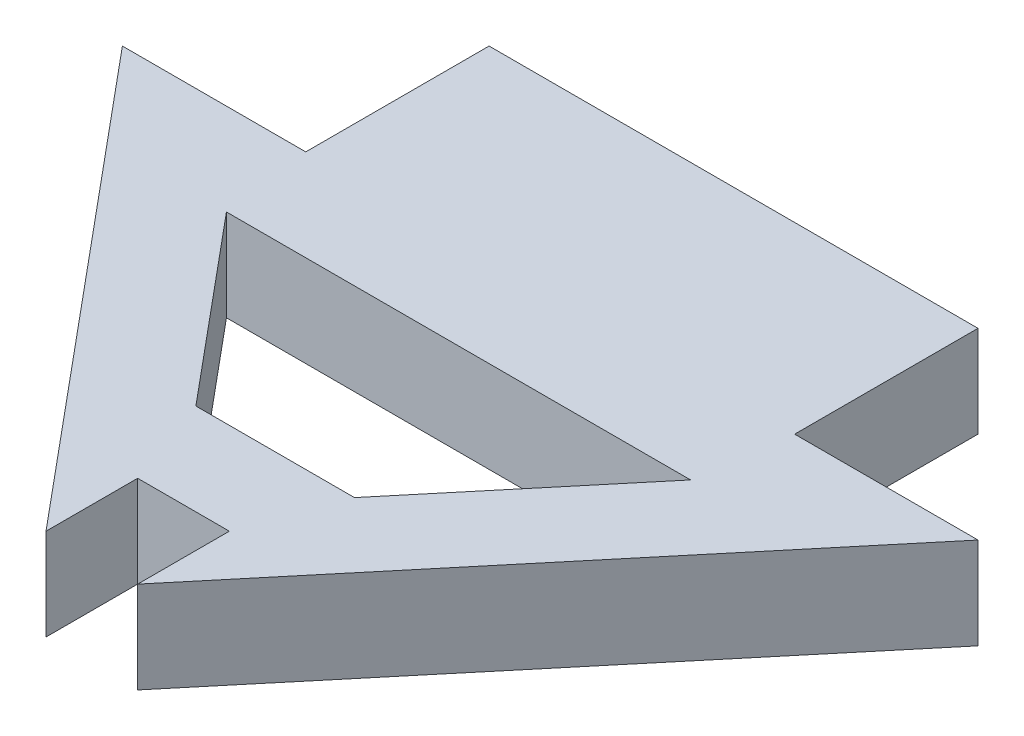
SolidWorks part; units mm, degrees
material "Custom Plastic"
ref_plane "Front Plane" through (0, 0, 0) normal (0, 0, 1) x (1, 0, 0)
ref_plane "Top Plane" through (0, 0, 0) normal (0, 1, 0) x (1, 0, 0)
ref_plane "Right Plane" through (0, 0, 0) normal (1, 0, 0) x (0, 0, -1)
sketch "Sketch1" plane through (0, 0, 0) normal (0, 1, 0) x (1, 0, 0)
  line L0 (22.0795, 3.0287) -> (16.0795, 3.0287)
  line L1 (16.0795, 3.0287) -> (16.0795, 9.0287)
  line L2 (16.0795, 9.0287) -> (0.0795, 9.0287)
  line L3 (0.0795, 9.0287) -> (0.0795, 3.0287)
  line L4 (0.0795, 3.0287) -> (-5.9205, 3.0287)
  line L5 (-5.9205, 3.0287) -> (6.5795, -11.9713)
  line L6 (6.5795, -11.9713) -> (6.5795, -8.9713)
  line L7 (6.5795, -8.9713) -> (9.5795, -8.9713)
  line L8 (9.5795, -8.9713) -> (9.5795, -11.9713)
  line L9 (9.5795, -11.9713) -> (22.0795, 3.0287)
  line L10 (8.0795, 9.0287) -> (8.0795, -8.9713) construction
  line L11 (9.5795, -11.9713) -> (6.5795, -11.9713) construction
  line L12 (15.6744, 0.0287) -> (0.4846, 0.0287)
  line L13 (0.4846, 0.0287) -> (5.4846, -5.9713)
  line L14 (5.4846, -5.9713) -> (10.6744, -5.9713)
  line L15 (10.6744, -5.9713) -> (15.6744, 0.0287)
  point P12 (6.5795, -10.4713)
  dimension "D1" = 3
  dimension "D2" = 28
  dimension "D3" = 6
  dimension "D4" = 6
  dimension "D5" = 12
  dimension "D6" = 3
  dimension "D7" = 3
  dimension "D8" = 3
  dimension "D9" = 3
  dimension "D10" = 3
extrude "Boss-Extrude1" add sketch "Sketch1" along normal blind 3
